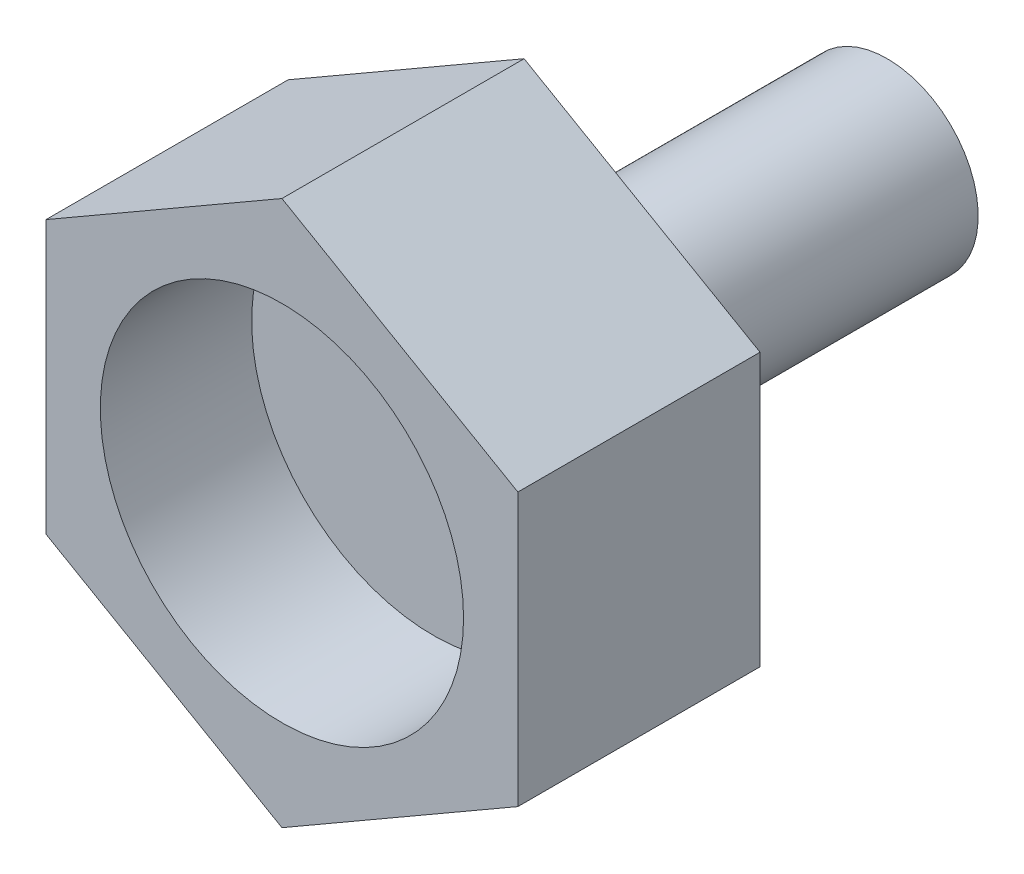
SolidWorks part; units mm, degrees
ref_plane "正面" through (0, 0, 0) normal (0, 0, 1) x (1, 0, 0)
ref_plane "平面" through (0, 0, 0) normal (0, 1, 0) x (1, 0, 0)
ref_plane "右側面" through (0, 0, 0) normal (1, 0, 0) x (0, 0, -1)
sketch "ｽｹｯﾁ2" plane through (0, 0, 0) normal (0, 0, 1) x (1, 0, 0)
  line L1 (3.8971, -2.25) -> (3.8971, 2.25)
  line L2 (3.8971, 2.25) -> (0, 4.5)
  line L3 (0, 4.5) -> (-3.8971, 2.25)
  line L4 (-3.8971, 2.25) -> (-3.8971, -2.25)
  line L5 (-3.8971, -2.25) -> (0, -4.5)
  line L6 (0, -4.5) -> (3.8971, -2.25)
  circle A0 centre (0, 0) radius 3.8971 construction
  dimension "D1" = 9
extrude "ﾎﾞｽ - 押し出し1" add sketch "ｽｹｯﾁ2" along normal blind 4
sketch "ｽｹｯﾁ3" plane through (0, 0, 0) normal (0, 0, -1) x (-1, 0, 0)
  circle A0 centre (0, 0) radius 1.5
  dimension "D1" = 3
extrude "ﾎﾞｽ - 押し出し2" add sketch "ｽｹｯﾁ3" along normal blind 6
cosmetic thread "ねじ山1" parameters "D2"=2.439
sketch "ｽｹｯﾁ4" plane through (0, 0, 4) normal (0, 0, 1) x (1, 0, 0)
  circle A0 centre (0, 0) radius 3
  dimension "D1" = 6
extrude "ｶｯﾄ - 押し出し1" cut sketch "ｽｹｯﾁ4" against normal blind 2.5
